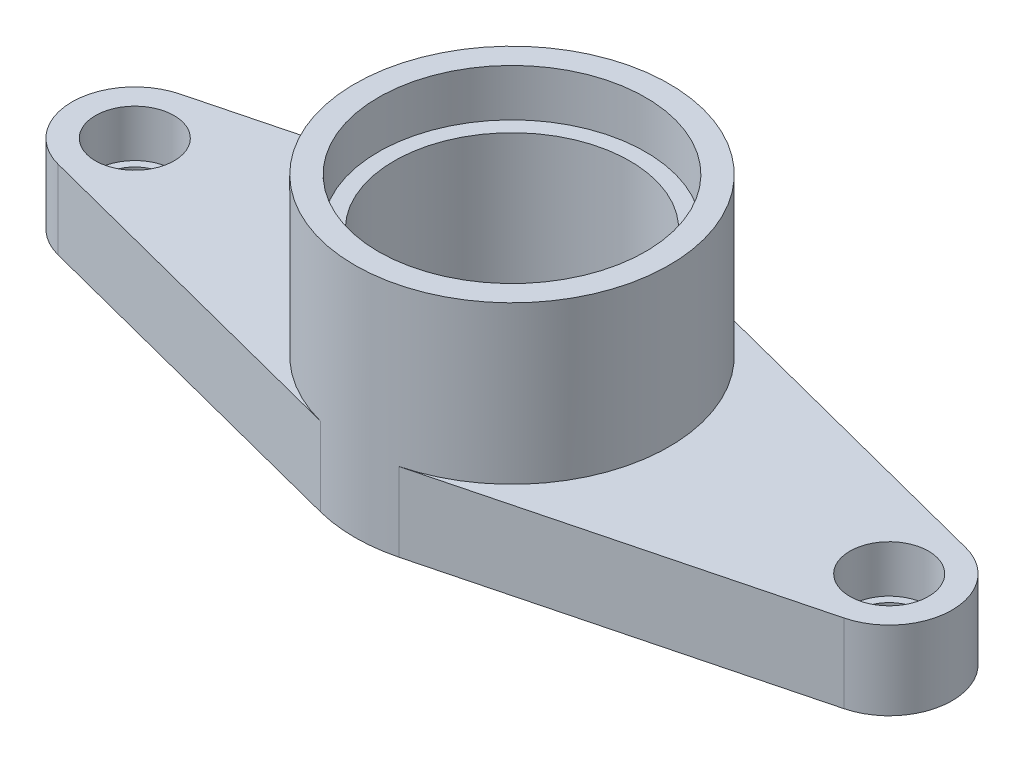
SolidWorks part; units mm, degrees
ref_plane "Front Plane" through (0, 0, 0) normal (0, 0, 1) x (1, 0, 0)
ref_plane "Top Plane" through (0, 0, 0) normal (0, 1, 0) x (1, 0, 0)
ref_plane "Right Plane" through (0, 0, 0) normal (1, 0, 0) x (0, 0, -1)
sketch "Sketch2" plane through (0, 0, 0) normal (0, 1, 0) x (1, 0, 0)
  line L0 (0, 71.2341) -> (0, -136.7991) construction
  line L1 (-165.6359, 0) -> (189.8187, 0) construction
  line L2 (-125, 19.3649) -> (-12.5, 48.4123)
  line L3 (-125, -19.3649) -> (-12.5, -48.4123)
  line L4 (125, -19.3649) -> (12.5, -48.4123)
  line L5 (125, 19.3649) -> (12.5, 48.4123)
  arc A0 (-12.5, -48.4123) -> (12.5, -48.4123) centre (0, 0) ccw
  arc A5 (-125, 19.3649) -> (-125, -19.3649) centre (-120, 0) ccw
  arc A8 (125, 19.3649) -> (125, -19.3649) centre (120, 0) cw
  arc A9 (12.5, 48.4123) -> (-12.5, 48.4123) centre (0, 0) ccw
  dimension "D1" = 100
  dimension "D6" = 120
extrude "Boss-Extrude3" add sketch "Sketch2" along normal blind 25 contours L3 A0 L4 A8 L5 A9 L2 A5
sketch "Sketch3" plane through (0, 25, 0) normal (0, 1, 0) x (1, 0, 0)
  line L0 (0, 63.4807) -> (0, -81.6181) construction
  circle A0 centre (-120, 0) radius 10
  circle A1 centre (120, 0) radius 10
extrude "Cut-Extrude1" cut sketch "Sketch3" against normal blind 25
sketch "Sketch4" plane through (0, 25, 0) normal (0, 1, 0) x (1, 0, 0)
  line L0 (0, 62.2914) -> (0, -73.5901) construction
  circle A0 centre (-120, 0) radius 12.5
  circle A1 centre (120, 0) radius 12.5
extrude "Cut-Extrude2" cut sketch "Sketch4" against normal blind 15
sketch "Sketch5" plane through (0, 0, 0) normal (0, 1, 0) x (1, 0, 0)
  circle A0 centre (0, 0) radius 50
extrude "Boss-Extrude5" add sketch "Sketch5" along normal blind 75
sketch "Sketch9" plane through (0, 75, 0) normal (0, 1, 0) x (1, 0, 0)
  circle A0 centre (0, 0) radius 42.5
extrude "Cut-Extrude5" cut sketch "Sketch9" against normal blind 15
sketch "Sketch10" plane through (0, 60, 0) normal (0, 1, 0) x (1, 0, 0)
  circle A0 centre (0, 0) radius 37.5
extrude "Cut-Extrude6" cut sketch "Sketch10" against normal blind 60
